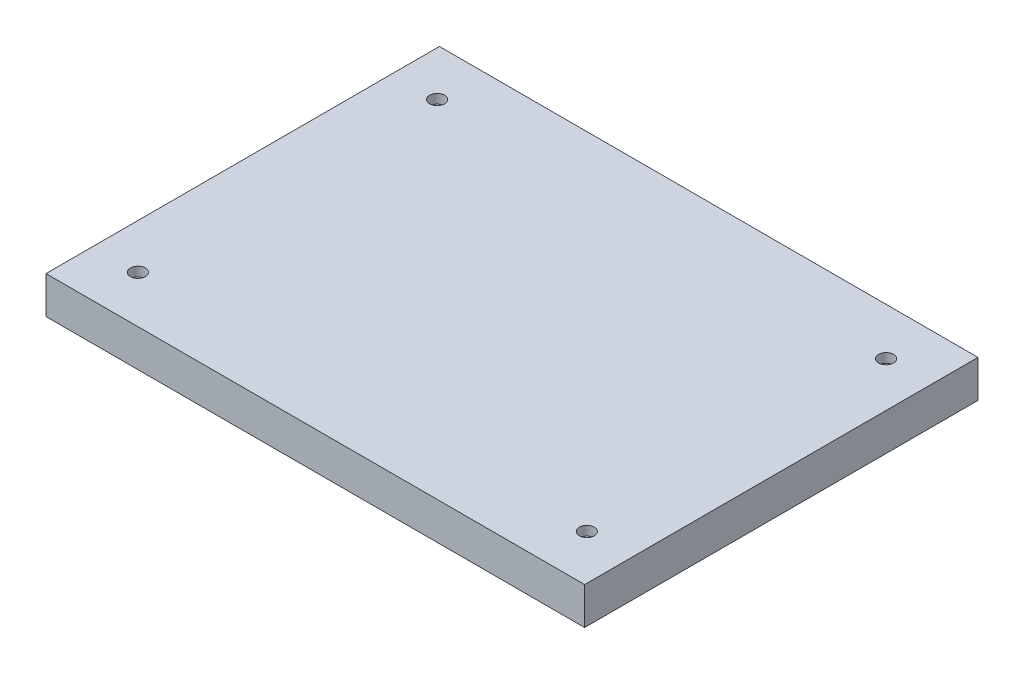
SolidWorks part; units mm, degrees
ref_plane "Front Plane" through (0, 0, 0) normal (0, 0, 1) x (1, 0, 0)
ref_plane "Top Plane" through (0, 0, 0) normal (0, 1, 0) x (1, 0, 0)
ref_plane "Right Plane" through (0, 0, 0) normal (1, 0, 0) x (0, 0, -1)
sketch "Sketch1" plane through (0, 0, 0) normal (0, 1, 0) x (1, 0, 0)
  line L0 (0, 0) -> (-179.959, 131.445) construction
  line L1 (-179.959, 131.445) -> (179.959, 131.445)
  line L2 (-179.959, 131.445) -> (-179.959, -131.445)
  line L3 (-179.959, -131.445) -> (179.959, -131.445)
  line L4 (179.959, 131.445) -> (179.959, -131.445)
  line L5 (0, 0) -> (179.959, -131.445) construction
  point P5 (178.6429, -130.4837)
  point P7 (106.8207, -78.0236)
  point P8 (179.959, -131.445)
  dimension "D1" = 359.918
  dimension "D2" = 262.89
extrude "Boss-Extrude1" add sketch "Sketch1" along normal mid plane 24.892
sketch "Sketch5" plane through (0, 12.446, 0) normal (0, 1, 0) x (1, 0, 0)
  line L0 (-150, -100) -> (-150, 100) construction
  line L1 (-150, 100) -> (150, 100) construction
  line L2 (150, 100) -> (150, -100) construction
  line L3 (150, -100) -> (-150, -100) construction
  line L4 (-150, 100) -> (0, 0) construction
  line L5 (0, 0) -> (150, -100) construction
  circle A0 centre (-150, 100) radius 5
  circle A1 centre (150, 100) radius 5
  circle A2 centre (150, -100) radius 5
  circle A3 centre (-150, -100) radius 5
  point P8 (152.2809, -105.7251)
  dimension "D3" = 10
  dimension "D1" = 300
  dimension "D2" = 200
extrude "Cut-Extrude1" cut sketch "Sketch5" against normal blind 6.223
